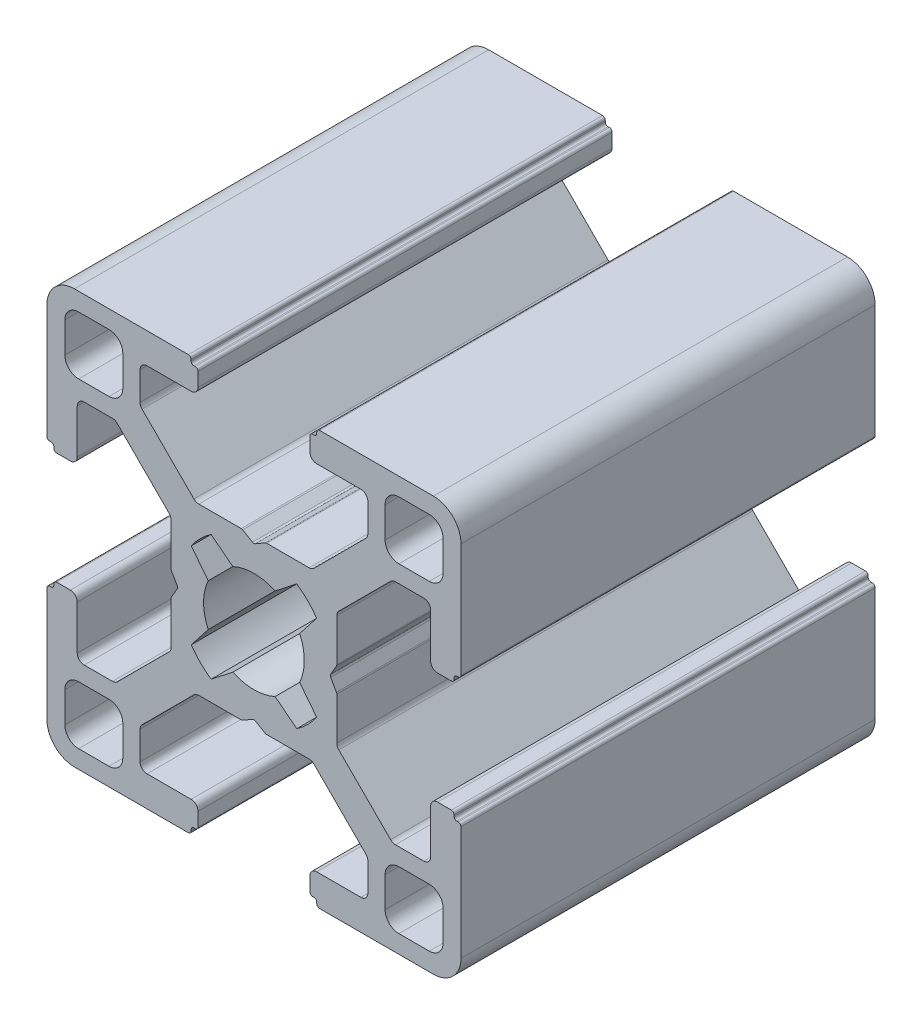
SolidWorks part; units mm, degrees
material "АД31Т ГОСТ 4784-97"
ref_plane "Спереди" through (0, 0, 0) normal (0, 0, 1) x (1, 0, 0)
ref_plane "Сверху" through (0, 0, 0) normal (0, 1, 0) x (1, 0, 0)
ref_plane "Справа" through (0, 0, 0) normal (1, 0, 0) x (0, 0, -1)
sketch "Эскиз1" plane through (0, 0, 0) normal (0, 0, 1) x (1, 0, 0)
  line L0 (-5.5577, 0.1) -> (-5.9732, 0.8196)
  line L2 (-4.541, 3.1031) -> (-3.3131, 1.5316)
  line L3 (3.9968, 6) -> (0.9196, 6)
  line L4 (14.3, -4.05) -> (13.3, -4.05)
  line L5 (-3.1031, 4.541) -> (-1.5316, 3.3131)
  line L6 (4.541, -3.1031) -> (3.3131, -1.5316)
  line L7 (3.1031, 4.541) -> (1.5316, 3.3131)
  line L8 (-14.3, 4.05) -> (-13.3, 4.05)
  line L9 (-15, 4.75) -> (-15, 13)
  line L10 (-14.8, 4.55) -> (-14.7, 4.55)
  line L11 (-14.5, 4.35) -> (-14.5, 4.25)
  line L12 (-12.8, 4.55) -> (-12.8, 7.75)
  line L13 (-13.7, 12.7) -> (-13.7, 10.5)
  line L14 (-12.7, 13.7) -> (-10.5, 13.7)
  line L15 (-12.7, 9.5) -> (-10.5, 9.5)
  line L16 (-9.5, 10.5) -> (-9.5, 12.7)
  line L17 (-6, 0.9196) -> (-6, 3.9968)
  line L18 (-12.3, 8.25) -> (-10.2532, 8.25)
  line L19 (-6.1464, 4.3504) -> (-9.8996, 8.1036)
  line L20 (-5.5577, -0.1) -> (-5.9732, -0.8196)
  line L21 (-0.1, -5.5577) -> (-0.8196, -5.9732)
  line L22 (-6, -3.9968) -> (-6, -0.9196)
  line L23 (-4.3504, 6.1464) -> (-8.1036, 9.8996)
  line L24 (-0.9196, -6) -> (-3.9968, -6)
  line L25 (4.541, 3.1031) -> (3.3131, 1.5316)
  line L26 (3.1031, -4.541) -> (1.5316, -3.3131)
  line L27 (-3.1031, -4.541) -> (-1.5316, -3.3131)
  line L28 (-4.541, -3.1031) -> (-3.3131, -1.5316)
  line L29 (0.1, -5.5577) -> (0.8196, -5.9732)
  line L36 (-8.25, 12.3) -> (-8.25, 10.2532)
  line L37 (-0.9196, 6) -> (-3.9968, 6)
  line L38 (-4.55, 12.8) -> (-7.75, 12.8)
  line L39 (-4.35, 14.5) -> (-4.25, 14.5)
  line L40 (-4.55, 14.8) -> (-4.55, 14.7)
  line L41 (-4.75, 15) -> (-13, 15)
  line L42 (-4.05, 14.3) -> (-4.05, 13.3)
  line L43 (0.1, 5.5577) -> (0.8196, 5.9732)
  line L44 (-0.9196, 6) -> (-3.9968, 6)
  line L45 (-0.1, 5.5577) -> (-0.8196, 5.9732)
  line L46 (-4.05, -14.3) -> (-4.05, -13.3)
  line L47 (-4.75, -15) -> (-13, -15)
  line L48 (-4.55, -14.8) -> (-4.55, -14.7)
  line L49 (-4.35, -14.5) -> (-4.25, -14.5)
  line L50 (-4.55, -12.8) -> (-7.75, -12.8)
  line L51 (-8.25, -12.3) -> (-8.25, -10.2532)
  line L52 (-4.3504, -6.1464) -> (-8.1036, -9.8996)
  line L53 (-6.1464, -4.3504) -> (-9.8996, -8.1036)
  line L54 (-12.3, -8.25) -> (-10.2532, -8.25)
  line L55 (-9.5, -10.5) -> (-9.5, -12.7)
  line L56 (-12.7, -9.5) -> (-10.5, -9.5)
  line L57 (-12.7, -13.7) -> (-10.5, -13.7)
  line L58 (-13.7, -12.7) -> (-13.7, -10.5)
  line L59 (-12.8, -4.55) -> (-12.8, -7.75)
  line L60 (-14.5, -4.35) -> (-14.5, -4.25)
  line L61 (-14.8, -4.55) -> (-14.7, -4.55)
  line L62 (-15, -4.75) -> (-15, -13)
  line L63 (-14.3, -4.05) -> (-13.3, -4.05)
  line L64 (15, -4.75) -> (15, -13)
  line L65 (14.8, -4.55) -> (14.7, -4.55)
  line L66 (14.5, -4.35) -> (14.5, -4.25)
  line L67 (12.8, -4.55) -> (12.8, -7.75)
  line L68 (13.7, -12.7) -> (13.7, -10.5)
  line L69 (12.7, -13.7) -> (10.5, -13.7)
  line L70 (12.7, -9.5) -> (10.5, -9.5)
  line L71 (9.5, -10.5) -> (9.5, -12.7)
  line L72 (12.3, -8.25) -> (10.2532, -8.25)
  line L73 (6.1464, -4.3504) -> (9.8996, -8.1036)
  line L74 (4.3504, -6.1464) -> (8.1036, -9.8996)
  line L75 (8.25, -12.3) -> (8.25, -10.2532)
  line L76 (4.55, -12.8) -> (7.75, -12.8)
  line L77 (4.35, -14.5) -> (4.25, -14.5)
  line L78 (4.55, -14.8) -> (4.55, -14.7)
  line L79 (4.75, -15) -> (13, -15)
  line L80 (4.05, -14.3) -> (4.05, -13.3)
  line L81 (4.05, 14.3) -> (4.05, 13.3)
  line L82 (4.75, 15) -> (13, 15)
  line L83 (4.55, 14.8) -> (4.55, 14.7)
  line L84 (4.35, 14.5) -> (4.25, 14.5)
  line L85 (4.55, 12.8) -> (7.75, 12.8)
  line L86 (8.25, 12.3) -> (8.25, 10.2532)
  line L89 (4.3504, 6.1464) -> (8.1036, 9.8996)
  line L90 (6, -3.9968) -> (6, -0.9196)
  line L91 (5.5577, -0.1) -> (5.9732, -0.8196)
  line L92 (6.1464, 4.3504) -> (9.8996, 8.1036)
  line L93 (12.3, 8.25) -> (10.2532, 8.25)
  line L94 (6, 0.9196) -> (6, 3.9968)
  line L95 (9.5, 10.5) -> (9.5, 12.7)
  line L96 (12.7, 9.5) -> (10.5, 9.5)
  line L97 (12.7, 13.7) -> (10.5, 13.7)
  line L98 (13.7, 12.7) -> (13.7, 10.5)
  line L99 (12.8, 4.55) -> (12.8, 7.75)
  line L100 (14.5, 4.35) -> (14.5, 4.25)
  line L101 (14.8, 4.55) -> (14.7, 4.55)
  line L102 (15, 4.75) -> (15, 13)
  line L103 (14.3, 4.05) -> (13.3, 4.05)
  line L104 (5.5577, 0.1) -> (5.9732, 0.8196)
  line L105 (-0.9196, -6) -> (-3.9968, -6)
  line L106 (3.9968, -6) -> (0.9196, -6)
  arc A0 (-13, 15) -> (-15, 13) centre (-13, 13) ccw
  arc A1 (-10.5, 13.7) -> (-9.5, 12.7) centre (-10.5, 12.7) cw
  arc A2 (-10.5, 9.5) -> (-9.5, 10.5) centre (-10.5, 10.5) ccw
  arc A3 (-13.7, 10.5) -> (-12.7, 9.5) centre (-12.7, 10.5) ccw
  arc A4 (-13.7, 12.7) -> (-12.7, 13.7) centre (-12.7, 12.7) cw
  arc A5 (-3.3624, 1.42) -> (-3.3624, -1.42) centre (0, 0) ccw
  arc A6 (-4.541, -3.1031) -> (-3.1031, -4.541) centre (0, 0) ccw
  arc A7 (-1.42, -3.3624) -> (1.42, -3.3624) centre (0, 0) ccw
  arc A8 (3.1031, -4.541) -> (4.541, -3.1031) centre (0, 0) ccw
  arc A9 (3.3624, -1.42) -> (3.3624, 1.42) centre (0, 0) ccw
  arc A10 (4.541, 3.1031) -> (3.1031, 4.541) centre (0, 0) ccw
  arc A11 (1.42, 3.3624) -> (-1.42, 3.3624) centre (0, 0) ccw
  arc A12 (-3.1031, 4.541) -> (-4.541, 3.1031) centre (0, 0) ccw
  arc A13 (-14.5, 4.25) -> (-14.3, 4.05) centre (-14.3, 4.25) ccw
  arc A14 (-14.7, 4.55) -> (-14.5, 4.35) centre (-14.7, 4.35) cw
  arc A15 (-14.8, 4.55) -> (-15, 4.75) centre (-14.8, 4.75) cw
  arc A16 (-13.3, 4.05) -> (-12.8, 4.55) centre (-13.3, 4.55) ccw
  arc A17 (-6.1464, 4.3504) -> (-6, 3.9968) centre (-6.5, 3.9968) cw
  arc A18 (-9.8996, 8.1036) -> (-10.2532, 8.25) centre (-10.2532, 7.75) ccw
  arc A19 (-12.8, 7.75) -> (-12.3, 8.25) centre (-12.3, 7.75) cw
  arc A20 (-5.9732, 0.8196) -> (-6, 0.9196) centre (-5.8, 0.9196) cw
  arc A21 (-5.5577, -0.1) -> (-5.5577, 0.1) centre (-5.7309, 0) ccw
  arc A22 (-5.9732, -0.8196) -> (-6, -0.9196) centre (-5.8, -0.9196) ccw
  arc A23 (-7.75, 12.8) -> (-8.25, 12.3) centre (-7.75, 12.3) ccw
  arc A24 (-8.1036, 9.8996) -> (-8.25, 10.2532) centre (-7.75, 10.2532) cw
  arc A25 (-4.3504, 6.1464) -> (-3.9968, 6) centre (-3.9968, 6.5) ccw
  arc A26 (-4.05, 13.3) -> (-4.55, 12.8) centre (-4.55, 13.3) cw
  arc A27 (-4.55, 14.8) -> (-4.75, 15) centre (-4.75, 14.8) ccw
  arc A28 (-4.55, 14.7) -> (-4.35, 14.5) centre (-4.35, 14.7) ccw
  arc A29 (-4.25, 14.5) -> (-4.05, 14.3) centre (-4.25, 14.3) cw
  arc A30 (0.8196, 5.9732) -> (0.9196, 6) centre (0.9196, 5.8) cw
  arc A31 (0.1, 5.5577) -> (-0.1, 5.5577) centre (0, 5.7309) cw
  arc A32 (-0.8196, 5.9732) -> (-0.9196, 6) centre (-0.9196, 5.8) ccw
  arc A33 (-4.25, -14.5) -> (-4.05, -14.3) centre (-4.25, -14.3) ccw
  arc A34 (-4.55, -14.7) -> (-4.35, -14.5) centre (-4.35, -14.7) cw
  arc A35 (-4.55, -14.8) -> (-4.75, -15) centre (-4.75, -14.8) cw
  arc A36 (-4.05, -13.3) -> (-4.55, -12.8) centre (-4.55, -13.3) ccw
  arc A37 (-4.3504, -6.1464) -> (-3.9968, -6) centre (-3.9968, -6.5) cw
  arc A38 (-8.1036, -9.8996) -> (-8.25, -10.2532) centre (-7.75, -10.2532) ccw
  arc A39 (-7.75, -12.8) -> (-8.25, -12.3) centre (-7.75, -12.3) cw
  arc A40 (-12.8, -7.75) -> (-12.3, -8.25) centre (-12.3, -7.75) ccw
  arc A41 (-9.8996, -8.1036) -> (-10.2532, -8.25) centre (-10.2532, -7.75) cw
  arc A42 (-6.1464, -4.3504) -> (-6, -3.9968) centre (-6.5, -3.9968) ccw
  arc A43 (-13.3, -4.05) -> (-12.8, -4.55) centre (-13.3, -4.55) cw
  arc A44 (-14.8, -4.55) -> (-15, -4.75) centre (-14.8, -4.75) ccw
  arc A45 (-14.7, -4.55) -> (-14.5, -4.35) centre (-14.7, -4.35) ccw
  arc A46 (-14.5, -4.25) -> (-14.3, -4.05) centre (-14.3, -4.25) cw
  arc A47 (-13.7, -12.7) -> (-12.7, -13.7) centre (-12.7, -12.7) ccw
  arc A48 (-13.7, -10.5) -> (-12.7, -9.5) centre (-12.7, -10.5) cw
  arc A49 (-10.5, -9.5) -> (-9.5, -10.5) centre (-10.5, -10.5) cw
  arc A50 (-10.5, -13.7) -> (-9.5, -12.7) centre (-10.5, -12.7) ccw
  arc A51 (-13, -15) -> (-15, -13) centre (-13, -13) cw
  arc A52 (13, -15) -> (15, -13) centre (13, -13) ccw
  arc A53 (10.5, -13.7) -> (9.5, -12.7) centre (10.5, -12.7) cw
  arc A54 (10.5, -9.5) -> (9.5, -10.5) centre (10.5, -10.5) ccw
  arc A55 (13.7, -10.5) -> (12.7, -9.5) centre (12.7, -10.5) ccw
  arc A56 (13.7, -12.7) -> (12.7, -13.7) centre (12.7, -12.7) cw
  arc A57 (14.5, -4.25) -> (14.3, -4.05) centre (14.3, -4.25) ccw
  arc A58 (14.7, -4.55) -> (14.5, -4.35) centre (14.7, -4.35) cw
  arc A59 (14.8, -4.55) -> (15, -4.75) centre (14.8, -4.75) cw
  arc A60 (13.3, -4.05) -> (12.8, -4.55) centre (13.3, -4.55) ccw
  arc A61 (6.1464, -4.3504) -> (6, -3.9968) centre (6.5, -3.9968) cw
  arc A62 (9.8996, -8.1036) -> (10.2532, -8.25) centre (10.2532, -7.75) ccw
  arc A63 (12.8, -7.75) -> (12.3, -8.25) centre (12.3, -7.75) cw
  arc A64 (7.75, -12.8) -> (8.25, -12.3) centre (7.75, -12.3) ccw
  arc A65 (8.1036, -9.8996) -> (8.25, -10.2532) centre (7.75, -10.2532) cw
  arc A66 (4.3504, -6.1464) -> (3.9968, -6) centre (3.9968, -6.5) ccw
  arc A67 (4.05, -13.3) -> (4.55, -12.8) centre (4.55, -13.3) cw
  arc A68 (4.55, -14.8) -> (4.75, -15) centre (4.75, -14.8) ccw
  arc A69 (4.55, -14.7) -> (4.35, -14.5) centre (4.35, -14.7) ccw
  arc A70 (4.25, -14.5) -> (4.05, -14.3) centre (4.25, -14.3) cw
  arc A71 (4.25, 14.5) -> (4.05, 14.3) centre (4.25, 14.3) ccw
  arc A72 (4.55, 14.7) -> (4.35, 14.5) centre (4.35, 14.7) cw
  arc A73 (4.55, 14.8) -> (4.75, 15) centre (4.75, 14.8) cw
  arc A74 (4.05, 13.3) -> (4.55, 12.8) centre (4.55, 13.3) ccw
  arc A75 (4.3504, 6.1464) -> (3.9968, 6) centre (3.9968, 6.5) cw
  arc A76 (8.1036, 9.8996) -> (8.25, 10.2532) centre (7.75, 10.2532) ccw
  arc A77 (7.75, 12.8) -> (8.25, 12.3) centre (7.75, 12.3) cw
  arc A78 (5.9732, -0.8196) -> (6, -0.9196) centre (5.8, -0.9196) cw
  arc A79 (5.5577, -0.1) -> (5.5577, 0.1) centre (5.7309, 0) cw
  arc A80 (5.9732, 0.8196) -> (6, 0.9196) centre (5.8, 0.9196) ccw
  arc A81 (12.8, 7.75) -> (12.3, 8.25) centre (12.3, 7.75) ccw
  arc A82 (9.8996, 8.1036) -> (10.2532, 8.25) centre (10.2532, 7.75) cw
  arc A83 (6.1464, 4.3504) -> (6, 3.9968) centre (6.5, 3.9968) ccw
  arc A84 (13.3, 4.05) -> (12.8, 4.55) centre (13.3, 4.55) cw
  arc A85 (14.8, 4.55) -> (15, 4.75) centre (14.8, 4.75) ccw
  arc A86 (14.7, 4.55) -> (14.5, 4.35) centre (14.7, 4.35) ccw
  arc A87 (14.5, 4.25) -> (14.3, 4.05) centre (14.3, 4.25) cw
  arc A88 (3.1031, 4.541) -> (4.541, 3.1031) centre (0, 0) cw
  arc A89 (4.541, -3.1031) -> (3.1031, -4.541) centre (0, 0) cw
  arc A90 (3.3624, 1.42) -> (3.3624, -1.42) centre (0, 0) cw
  arc A91 (13.7, 12.7) -> (12.7, 13.7) centre (12.7, 12.7) ccw
  arc A92 (13.7, 10.5) -> (12.7, 9.5) centre (12.7, 10.5) cw
  arc A93 (10.5, 9.5) -> (9.5, 10.5) centre (10.5, 10.5) cw
  arc A94 (10.5, 13.7) -> (9.5, 12.7) centre (10.5, 12.7) ccw
  arc A95 (13, 15) -> (15, 13) centre (13, 13) cw
  arc A96 (-0.8196, -5.9732) -> (-0.9196, -6) centre (-0.9196, -5.8) cw
  arc A97 (0.1, -5.5577) -> (-0.1, -5.5577) centre (0, -5.7309) ccw
  arc A98 (0.8196, -5.9732) -> (0.9196, -6) centre (0.9196, -5.8) ccw
  arc A99 (-3.3131, 1.5316) -> (-3.3131, -1.5316) centre (0, 0) ccw
  arc A100 (3.3131, 1.5316) -> (3.3131, -1.5316) centre (0, 0) cw
  arc A101 (3.1031, 4.541) -> (4.541, 3.1031) centre (0, 0) cw
  arc A102 (3.1031, -4.541) -> (4.541, -3.1031) centre (0, 0) ccw
  arc A103 (3.1031, -4.541) -> (4.541, -3.1031) centre (0, 0) ccw
  arc A104 (-3.1031, -4.541) -> (-4.541, -3.1031) centre (0, 0) cw
  arc A105 (1.42, -3.3624) -> (-1.42, -3.3624) centre (0, 0) cw
  arc A106 (4.541, -3.1031) -> (3.1031, -4.541) centre (0, 0) cw
  arc A107 (3.3131, -1.5316) -> (3.3131, 1.5316) centre (0, 0) ccw
  arc A108 (1.5316, -3.3131) -> (-1.5316, -3.3131) centre (0, 0) cw
  arc A109 (1.5316, 3.3131) -> (-1.5316, 3.3131) centre (0, 0) ccw
  arc A110 (-1.5316, 3.3131) -> (1.5316, 3.3131) centre (0, 0) cw
  arc A111 (-1.5316, -3.3131) -> (1.5316, -3.3131) centre (0, 0) ccw
  arc A112 (-3.3131, -1.5316) -> (-3.3131, 1.5316) centre (0, 0) cw
  point P26 (-9.5, 9.5)
  point P43 (-3.8891, 3.8891)
  point P63 (-15, 4.55)
  point P74 (-6, 0.866)
  point P101 (-4.55, 15)
  point P110 (-0.866, 6)
  point P168 (-4.55, -15)
  point P169 (-15, -4.55)
  point P170 (-3.8891, -3.8891)
  point P171 (-9.5, -9.5)
  point P294 (9.5, -9.5)
  point P295 (3.8891, -3.8891)
  point P296 (15, -4.55)
  point P297 (4.55, -15)
  point P298 (4.55, 15)
  point P299 (6, 0.866)
  point P300 (15, 4.55)
  point P301 (3.8891, 3.8891)
  point P302 (9.5, 9.5)
  point P311 (-0.866, -6)
extrude "Бобышка-Вытянуть1" add sketch "Эскиз1" along normal blind 30 contours L29 A98 L106 A66 L74 A65 L75 A64 L76 A67 L80 A70 L77 A69 L78 A68 L79 A52 L64 A59 L65 A58 L66 A57 L4 A60 L67 A63 L72 A62 L73 A61 L90 A78 L91 A79 L104 A80 L94 A83 L92 A82 L93 A81 L99 A84 L103 A87 L100 A86 L101
